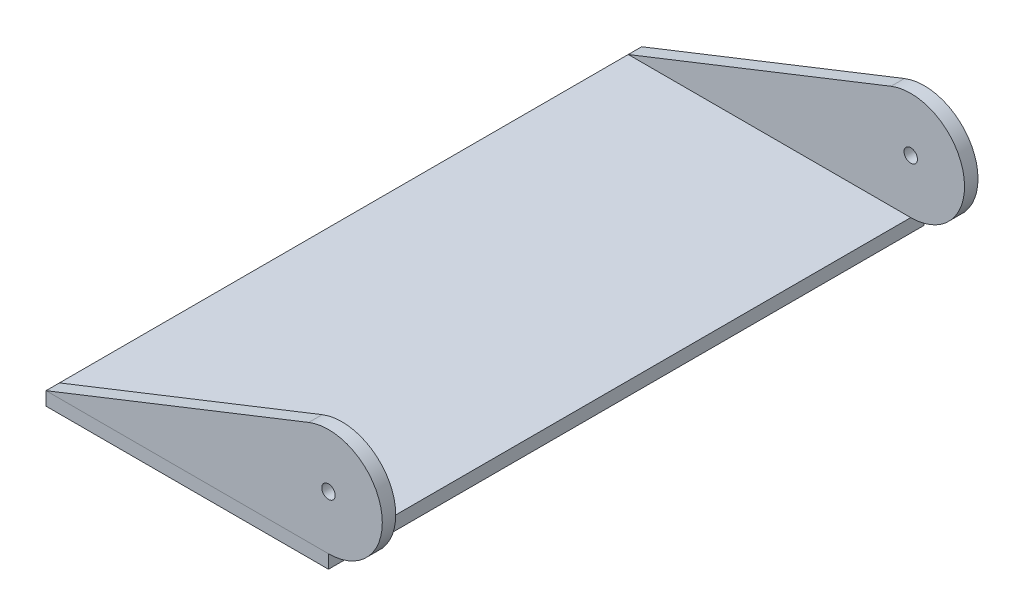
SolidWorks part; units mm, degrees
ref_plane "Front Plane" through (0, 0, 0) normal (0, 0, 1) x (1, 0, 0)
ref_plane "Top Plane" through (0, 0, 0) normal (0, 1, 0) x (1, 0, 0)
ref_plane "Right Plane" through (0, 0, 0) normal (1, 0, 0) x (0, 0, -1)
sketch "Sketch1" plane through (0, 0, 0) normal (0, 1, 0) x (1, 0, 0)
  line L1 (-0.4158, -69.7752) -> (32.9217, -69.7752)
  line L2 (-0.4158, -69.7752) -> (-0.4158, 0.5248)
  line L3 (-0.4158, 0.5248) -> (32.9217, 0.5248)
  line L4 (32.9217, -69.7752) -> (32.9217, 0.5248)
  dimension "D1" = 33.3375
  dimension "D2" = 70.3
extrude "Boss-Extrude1" add sketch "Sketch1" along normal blind 1.5875 contours L3 L4 L1 L2
sketch "Sketch3" plane through (0, 0, 69.7752) normal (0, 0, 1) x (1, 0, 0)
  line L0 (32.9217, 1.5875) -> (32.9217, 7.9375) construction
  line L1 (-0.4158, 1.5875) -> (30.5874, 13.8429)
  line L3 (-0.4158, 1.5875) -> (32.9217, 1.5875)
  circle A1 centre (32.9217, 7.9375) radius 6.35
  circle A2 centre (32.9217, 7.9375) radius 0.7937
  dimension "D2" = 1.5875
  dimension "D1" = 6.35
extrude "Boss-Extrude2" add sketch "Sketch3" against normal up to surface (70.3 mm away) separate body
sketch "Sketch4" plane through (-0.4158, 0, 0) normal (-1, 0, 0) x (0, 0, 1)
  line L5 (69.7752, 1.5875) -> (-0.5248, 1.5875) construction
  line L6 (1.0627, 1.5875) -> (68.1877, 1.5875)
  line L7 (1.0627, 1.5875) -> (1.0627, 14.2875)
  line L8 (1.0627, 14.2875) -> (68.1877, 14.2875)
  line L9 (68.1877, 1.5875) -> (68.1877, 14.2875)
  line L10 (69.7752, 14.2875) -> (-0.5248, 14.2875) construction
  line L11 (-0.5248, 1.5875) -> (-0.5248, 13.8429) construction
  line L12 (69.7752, 1.5875) -> (69.7752, 13.8429) construction
  dimension "D1" = 1.5875
  dimension "D2" = 1.5875
extrude "Cut-Extrude1" cut sketch "Sketch4" against normal through all
